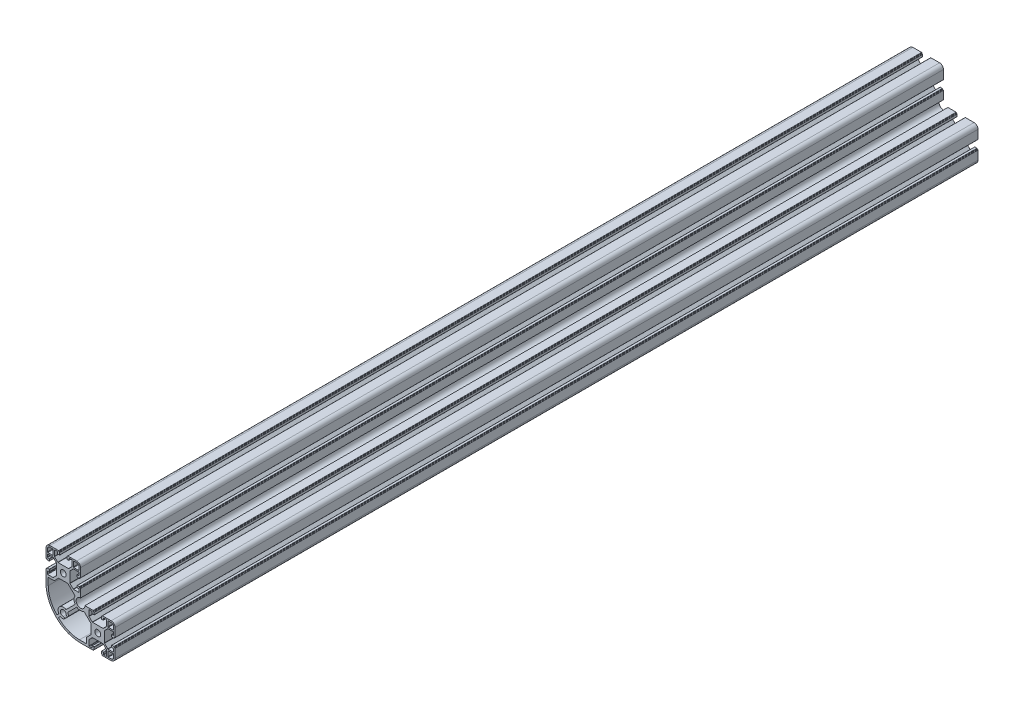
SolidWorks part; units mm, degrees
material "6063 T5"
ref_plane "Спереди" through (0, 0, 0) normal (0, 0, 1) x (1, 0, 0)
ref_plane "Сверху" through (0, 0, 0) normal (0, 1, 0) x (1, 0, 0)
ref_plane "Справа" through (0, 0, 0) normal (1, 0, 0) x (0, 0, -1)
sketch "Эскиз1" plane through (0, 0, 0) normal (0, 0, 1) x (1, 0, 0)
  line L0 (-19.98, 20.5457) -> (20.02, 20.5457) construction
  line L1 (-20, 10.25) -> (-20, 15.5)
  line L2 (-15.5, 20) -> (-10.25, 20)
  line L3 (10.25, 20) -> (15.5, 20)
  line L4 (-12.3, 11.8) -> (-17.8, 11.8)
  line L5 (-11.8, 12.3) -> (-11.8, 17.8)
  line L6 (-12.3, 18.3) -> (-15.5, 18.3)
  line L7 (-18.3, 12.3) -> (-18.3, 15.5)
  line L8 (20, 15.5) -> (20, 10.25)
  line L9 (11.8, 12.3) -> (11.8, 17.8)
  line L10 (12.3, 11.8) -> (17.8, 11.8)
  line L11 (18.3, 12.3) -> (18.3, 15.5)
  line L12 (12.3, 18.3) -> (15.5, 18.3)
  line L13 (0, 0) -> (0, -40) construction
  line L14 (0, -40) -> (40, -40) construction
  line L19 (0, -40) -> (40, 0) construction
  line L20 (0, 0) -> (-20, -10.25) construction
  line L25 (0, 0) -> (-11.8, 12.3) construction
  line L26 (0, 0) -> (12.3, 11.8) construction
  line L27 (60, -55.5) -> (60, -50.25)
  line L28 (50.25, -60) -> (55.5, -60)
  line L29 (58.3, -52.3) -> (58.3, -55.5)
  line L30 (52.3, -58.3) -> (55.5, -58.3)
  line L31 (51.8, -52.3) -> (51.8, -57.8)
  line L32 (52.3, -51.8) -> (57.8, -51.8)
  line L33 (51.8, -27.7) -> (51.8, -22.2)
  line L34 (52.3, -21.7) -> (55.5, -21.7)
  line L35 (58.3, -27.7) -> (58.3, -24.5)
  line L36 (52.3, -28.2) -> (57.8, -28.2)
  line L37 (55.5, -20) -> (50.25, -20)
  line L38 (0, 0) -> (-10.25, 20) construction
  line L39 (60, -29.75) -> (60, -24.5)
  line L40 (-19.9447, 33.6) -> (60.0553, 33.6) construction
  line L41 (-20, -10.25) -> (-20, -20)
  line L42 (20, -60) -> (29.75, -60)
  line L43 (-17.4, -12.85) -> (-17.4, -21.15)
  line L44 (-7.3211, -45.4826) -> (-5.0611, -43.2226)
  line L45 (-17.4, -12.85) -> (-10.623, -12.85)
  line L46 (-10.623, -12.85) -> (-5.373, -7.6)
  line L47 (-5.373, -7.6) -> (5.373, -7.6)
  line L48 (5.373, -7.6) -> (13.7014, -15.9284)
  line L49 (20, -10.25) -> (20, -14.9)
  line L50 (25.1, -20) -> (29.75, -20)
  line L51 (3.2226, -34.9389) -> (13.8577, -24.3038)
  line L52 (-5.4826, -47.3211) -> (-3.2226, -45.0611)
  line L53 (27.15, -57.4) -> (18.85, -57.4)
  line L54 (27.15, -57.4) -> (27.15, -50.623)
  line L55 (27.15, -50.623) -> (32.4, -45.373)
  line L56 (32.4, -45.373) -> (32.4, -34.627)
  line L57 (32.4, -34.627) -> (24.0716, -26.2986)
  line L58 (5.0611, -36.7774) -> (15.6962, -26.1423)
  arc A0 (-20, 15.5) -> (-15.5, 20) centre (-15.5, 15.5) cw
  arc A1 (-15.5, 18.3) -> (-18.3, 15.5) centre (-15.5, 15.5) ccw
  arc A2 (-17.8, 11.8) -> (-18.3, 12.3) centre (-17.8, 12.3) cw
  arc A3 (-12.3, 11.8) -> (-11.8, 12.3) centre (-12.3, 12.3) ccw
  arc A4 (-11.8, 17.8) -> (-12.3, 18.3) centre (-12.3, 17.8) ccw
  circle A5 centre (0, 0) radius 3.4
  arc A6 (15.5, 20) -> (20, 15.5) centre (15.5, 15.5) cw
  arc A7 (18.3, 15.5) -> (15.5, 18.3) centre (15.5, 15.5) ccw
  arc A8 (11.8, 17.8) -> (12.3, 18.3) centre (12.3, 17.8) cw
  arc A9 (11.8, 12.3) -> (12.3, 11.8) centre (12.3, 12.3) ccw
  arc A10 (17.8, 11.8) -> (18.3, 12.3) centre (17.8, 12.3) ccw
  circle A11 centre (40, -40) radius 3.4
  arc A16 (55.5, -60) -> (60, -55.5) centre (55.5, -55.5) ccw
  arc A21 (58.3, -55.5) -> (55.5, -58.3) centre (55.5, -55.5) cw
  arc A22 (51.8, -57.8) -> (52.3, -58.3) centre (52.3, -57.8) ccw
  arc A23 (51.8, -52.3) -> (52.3, -51.8) centre (52.3, -52.3) cw
  arc A24 (57.8, -51.8) -> (58.3, -52.3) centre (57.8, -52.3) cw
  arc A25 (52.3, -28.2) -> (51.8, -27.7) centre (52.3, -27.7) cw
  arc A26 (51.8, -22.2) -> (52.3, -21.7) centre (52.3, -22.2) cw
  arc A27 (55.5, -21.7) -> (58.3, -24.5) centre (55.5, -24.5) cw
  arc A28 (57.8, -28.2) -> (58.3, -27.7) centre (57.8, -27.7) ccw
  arc A29 (60, -24.5) -> (55.5, -20) centre (55.5, -24.5) ccw
  arc A30 (-20, -20) -> (20, -60) centre (20, -20) ccw
  arc A31 (-17.4, -21.15) -> (-7.3211, -45.4826) centre (17.0115, -21.15) ccw
  arc A32 (20, -14.9) -> (25.1, -20) centre (20, -20) ccw
  arc A33 (13.7014, -15.9284) -> (13.8577, -24.3038) centre (20, -20) ccw
  arc A34 (-5.0611, -43.2226) -> (3.2226, -34.9389) centre (0, -40) cw
  arc A36 (18.85, -57.4) -> (-5.4826, -47.3211) centre (18.85, -22.9885) cw
  arc A37 (24.0716, -26.2986) -> (15.6962, -26.1423) centre (20, -20) cw
  arc A38 (0, -43.4) -> (3.4, -40) centre (0, -40) cw
  arc A39 (3.4, -40) -> (6, -40) centre (4.7, -40) ccw
  arc A40 (5.0611, -36.7774) -> (6, -40) centre (0, -40) cw
  arc A41 (-3.2226, -45.0611) -> (0, -46) centre (0, -40) ccw
  arc A42 (0, -43.4) -> (0, -46) centre (0, -44.7) cw
  point P5 (0, 0)
  point P23 (0, 0)
  point P103 (0, -7.6)
  line B0 (-20, 10.25) -> (-20, 5.4)
  line B1 (-19.7, 5.1) -> (-19.3, 5.1)
  line B2 (-19, 4.8) -> (-19, 4.4)
  line B3 (-18.7, 4.1) -> (-16.3, 4.1)
  line B4 (-16, 4.4) -> (-16, 6.3)
  line B5 (-16.3, 6.6) -> (-18, 6.6)
  line B6 (-18.5, 7.1) -> (-18.5, 9.75)
  line B7 (-18, 10.25) -> (-11.9071, 10.25)
  line B8 (-11.5536, 10.1036) -> (-7.8464, 6.3964)
  line B9 (-7.7, 6.0429) -> (-7.7, -6.0429)
  line B10 (-7.7, 0) -> (-20, 0) construction
  line B11 (-11.5536, -10.1036) -> (-7.8464, -6.3964)
  line B12 (-18, -10.25) -> (-11.9071, -10.25)
  line B13 (-18.5, -7.1) -> (-18.5, -9.75)
  line B14 (-16.3, -6.6) -> (-18, -6.6)
  line B15 (-16, -4.4) -> (-16, -6.3)
  line B16 (-18.7, -4.1) -> (-16.3, -4.1)
  line B17 (-19, -4.8) -> (-19, -4.4)
  line B18 (-19.7, -5.1) -> (-19.3, -5.1)
  line B19 (-20, -10.25) -> (-20, -5.4)
  arc B20 (-16, 6.3) -> (-16.3, 6.6) centre (-16.3, 6.3) ccw
  arc B21 (-16.3, 4.1) -> (-16, 4.4) centre (-16.3, 4.4) ccw
  arc B22 (-19, 4.4) -> (-18.7, 4.1) centre (-18.7, 4.4) ccw
  arc B23 (-19.3, 5.1) -> (-19, 4.8) centre (-19.3, 4.8) cw
  arc B24 (-20, 5.4) -> (-19.7, 5.1) centre (-19.7, 5.4) ccw
  arc B25 (-7.8464, 6.3964) -> (-7.7, 6.0429) centre (-8.2, 6.0429) cw
  arc B26 (-11.9071, 10.25) -> (-11.5536, 10.1036) centre (-11.9071, 9.75) cw
  arc B27 (-18.5, 9.75) -> (-18, 10.25) centre (-18, 9.75) cw
  arc B28 (-18, 6.6) -> (-18.5, 7.1) centre (-18, 7.1) cw
  arc B29 (-18, -6.6) -> (-18.5, -7.1) centre (-18, -7.1) ccw
  arc B30 (-18.5, -9.75) -> (-18, -10.25) centre (-18, -9.75) ccw
  arc B31 (-11.9071, -10.25) -> (-11.5536, -10.1036) centre (-11.9071, -9.75) ccw
  arc B32 (-7.8464, -6.3964) -> (-7.7, -6.0429) centre (-8.2, -6.0429) ccw
  arc B33 (-20, -5.4) -> (-19.7, -5.1) centre (-19.7, -5.4) cw
  arc B34 (-19.3, -5.1) -> (-19, -4.8) centre (-19.3, -4.8) ccw
  arc B35 (-19, -4.4) -> (-18.7, -4.1) centre (-18.7, -4.4) cw
  arc B36 (-16.3, -4.1) -> (-16, -4.4) centre (-16.3, -4.4) cw
  arc B37 (-16, -6.3) -> (-16.3, -6.6) centre (-16.3, -6.3) cw
  line B38 (10.25, 20) -> (5.4, 20)
  line B39 (5.1, 19.7) -> (5.1, 19.3)
  line B40 (4.8, 19) -> (4.4, 19)
  line B41 (4.1, 18.7) -> (4.1, 16.3)
  line B42 (4.4, 16) -> (6.3, 16)
  line B43 (6.6, 16.3) -> (6.6, 18)
  line B44 (7.1, 18.5) -> (9.75, 18.5)
  line B45 (10.25, 18) -> (10.25, 11.9071)
  line B46 (10.1036, 11.5536) -> (6.3964, 7.8464)
  line B47 (6.0429, 7.7) -> (-6.0429, 7.7)
  line B48 (0, 7.7) -> (0, 20) construction
  line B49 (-10.1036, 11.5536) -> (-6.3964, 7.8464)
  line B50 (-10.25, 18) -> (-10.25, 11.9071)
  line B51 (-7.1, 18.5) -> (-9.75, 18.5)
  line B52 (-6.6, 16.3) -> (-6.6, 18)
  line B53 (-4.4, 16) -> (-6.3, 16)
  line B54 (-4.1, 18.7) -> (-4.1, 16.3)
  line B55 (-4.8, 19) -> (-4.4, 19)
  line B56 (-5.1, 19.7) -> (-5.1, 19.3)
  line B57 (-10.25, 20) -> (-5.4, 20)
  arc B58 (6.3, 16) -> (6.6, 16.3) centre (6.3, 16.3) ccw
  arc B59 (4.1, 16.3) -> (4.4, 16) centre (4.4, 16.3) ccw
  arc B60 (4.4, 19) -> (4.1, 18.7) centre (4.4, 18.7) ccw
  arc B61 (5.1, 19.3) -> (4.8, 19) centre (4.8, 19.3) cw
  arc B62 (5.4, 20) -> (5.1, 19.7) centre (5.4, 19.7) ccw
  arc B63 (6.3964, 7.8464) -> (6.0429, 7.7) centre (6.0429, 8.2) cw
  arc B64 (10.25, 11.9071) -> (10.1036, 11.5536) centre (9.75, 11.9071) cw
  arc B65 (9.75, 18.5) -> (10.25, 18) centre (9.75, 18) cw
  arc B66 (6.6, 18) -> (7.1, 18.5) centre (7.1, 18) cw
  arc B67 (-6.6, 18) -> (-7.1, 18.5) centre (-7.1, 18) ccw
  arc B68 (-9.75, 18.5) -> (-10.25, 18) centre (-9.75, 18) ccw
  arc B69 (-10.25, 11.9071) -> (-10.1036, 11.5536) centre (-9.75, 11.9071) ccw
  arc B70 (-6.3964, 7.8464) -> (-6.0429, 7.7) centre (-6.0429, 8.2) ccw
  arc B71 (-5.4, 20) -> (-5.1, 19.7) centre (-5.4, 19.7) cw
  arc B72 (-5.1, 19.3) -> (-4.8, 19) centre (-4.8, 19.3) ccw
  arc B73 (-4.4, 19) -> (-4.1, 18.7) centre (-4.4, 18.7) cw
  arc B74 (-4.1, 16.3) -> (-4.4, 16) centre (-4.4, 16.3) cw
  arc B75 (-6.3, 16) -> (-6.6, 16.3) centre (-6.3, 16.3) cw
  line B76 (20, -10.25) -> (20, -5.4)
  line B77 (19.7, -5.1) -> (19.3, -5.1)
  line B78 (19, -4.8) -> (19, -4.4)
  line B79 (18.7, -4.1) -> (16.3, -4.1)
  line B80 (16, -4.4) -> (16, -6.3)
  line B81 (16.3, -6.6) -> (18, -6.6)
  line B82 (18.5, -7.1) -> (18.5, -9.75)
  line B83 (18, -10.25) -> (11.9071, -10.25)
  line B84 (11.5536, -10.1036) -> (7.8464, -6.3964)
  line B85 (7.7, -6.0429) -> (7.7, 6.0429)
  line B86 (7.7, 0) -> (20, 0) construction
  line B87 (11.5536, 10.1036) -> (7.8464, 6.3964)
  line B88 (18, 10.25) -> (11.9071, 10.25)
  line B89 (18.5, 7.1) -> (18.5, 9.75)
  line B90 (16.3, 6.6) -> (18, 6.6)
  line B91 (16, 4.4) -> (16, 6.3)
  line B92 (18.7, 4.1) -> (16.3, 4.1)
  line B93 (19, 4.8) -> (19, 4.4)
  line B94 (19.7, 5.1) -> (19.3, 5.1)
  line B95 (20, 10.25) -> (20, 5.4)
  arc B96 (16, -6.3) -> (16.3, -6.6) centre (16.3, -6.3) ccw
  arc B97 (16.3, -4.1) -> (16, -4.4) centre (16.3, -4.4) ccw
  arc B98 (19, -4.4) -> (18.7, -4.1) centre (18.7, -4.4) ccw
  arc B99 (19.3, -5.1) -> (19, -4.8) centre (19.3, -4.8) cw
  arc B100 (20, -5.4) -> (19.7, -5.1) centre (19.7, -5.4) ccw
  arc B101 (7.8464, -6.3964) -> (7.7, -6.0429) centre (8.2, -6.0429) cw
  arc B102 (11.9071, -10.25) -> (11.5536, -10.1036) centre (11.9071, -9.75) cw
  arc B103 (18.5, -9.75) -> (18, -10.25) centre (18, -9.75) cw
  arc B104 (18, -6.6) -> (18.5, -7.1) centre (18, -7.1) cw
  arc B105 (18, 6.6) -> (18.5, 7.1) centre (18, 7.1) ccw
  arc B106 (18.5, 9.75) -> (18, 10.25) centre (18, 9.75) ccw
  arc B107 (11.9071, 10.25) -> (11.5536, 10.1036) centre (11.9071, 9.75) ccw
  arc B108 (7.8464, 6.3964) -> (7.7, 6.0429) centre (8.2, 6.0429) ccw
  arc B109 (20, 5.4) -> (19.7, 5.1) centre (19.7, 5.4) cw
  arc B110 (19.3, 5.1) -> (19, 4.8) centre (19.3, 4.8) ccw
  arc B111 (19, 4.4) -> (18.7, 4.1) centre (18.7, 4.4) cw
  arc B112 (16.3, 4.1) -> (16, 4.4) centre (16.3, 4.4) cw
  arc B113 (16, 6.3) -> (16.3, 6.6) centre (16.3, 6.3) cw
  line B114 (29.75, -20) -> (34.6, -20)
  line B115 (34.9, -20.3) -> (34.9, -20.7)
  line B116 (35.2, -21) -> (35.6, -21)
  line B117 (35.9, -21.3) -> (35.9, -23.7)
  line B118 (35.6, -24) -> (33.7, -24)
  line B119 (33.4, -23.7) -> (33.4, -22)
  line B120 (32.9, -21.5) -> (30.25, -21.5)
  line B121 (29.75, -22) -> (29.75, -28.0929)
  line B122 (29.8964, -28.4464) -> (33.6036, -32.1536)
  line B123 (33.9571, -32.3) -> (46.0429, -32.3)
  line B124 (40, -32.3) -> (40, -20) construction
  line B125 (50.1036, -28.4464) -> (46.3964, -32.1536)
  line B126 (50.25, -22) -> (50.25, -28.0929)
  line B127 (47.1, -21.5) -> (49.75, -21.5)
  line B128 (46.6, -23.7) -> (46.6, -22)
  line B129 (44.4, -24) -> (46.3, -24)
  line B130 (44.1, -21.3) -> (44.1, -23.7)
  line B131 (44.8, -21) -> (44.4, -21)
  line B132 (45.1, -20.3) -> (45.1, -20.7)
  line B133 (50.25, -20) -> (45.4, -20)
  arc B134 (33.7, -24) -> (33.4, -23.7) centre (33.7, -23.7) cw
  arc B135 (35.9, -23.7) -> (35.6, -24) centre (35.6, -23.7) cw
  arc B136 (35.6, -21) -> (35.9, -21.3) centre (35.6, -21.3) cw
  arc B137 (34.9, -20.7) -> (35.2, -21) centre (35.2, -20.7) ccw
  arc B138 (34.6, -20) -> (34.9, -20.3) centre (34.6, -20.3) cw
  arc B139 (33.6036, -32.1536) -> (33.9571, -32.3) centre (33.9571, -31.8) ccw
  arc B140 (29.75, -28.0929) -> (29.8964, -28.4464) centre (30.25, -28.0929) ccw
  arc B141 (30.25, -21.5) -> (29.75, -22) centre (30.25, -22) ccw
  arc B142 (33.4, -22) -> (32.9, -21.5) centre (32.9, -22) ccw
  arc B143 (46.6, -22) -> (47.1, -21.5) centre (47.1, -22) cw
  arc B144 (49.75, -21.5) -> (50.25, -22) centre (49.75, -22) cw
  arc B145 (50.25, -28.0929) -> (50.1036, -28.4464) centre (49.75, -28.0929) cw
  arc B146 (46.3964, -32.1536) -> (46.0429, -32.3) centre (46.0429, -31.8) cw
  arc B147 (45.4, -20) -> (45.1, -20.3) centre (45.4, -20.3) ccw
  arc B148 (45.1, -20.7) -> (44.8, -21) centre (44.8, -20.7) cw
  arc B149 (44.4, -21) -> (44.1, -21.3) centre (44.4, -21.3) ccw
  arc B150 (44.1, -23.7) -> (44.4, -24) centre (44.4, -23.7) ccw
  arc B151 (46.3, -24) -> (46.6, -23.7) centre (46.3, -23.7) ccw
  line B152 (50.25, -60) -> (45.4, -60)
  line B153 (45.1, -59.7) -> (45.1, -59.3)
  line B154 (44.8, -59) -> (44.4, -59)
  line B155 (44.1, -58.7) -> (44.1, -56.3)
  line B156 (44.4, -56) -> (46.3, -56)
  line B157 (46.6, -56.3) -> (46.6, -58)
  line B158 (47.1, -58.5) -> (49.75, -58.5)
  line B159 (50.25, -58) -> (50.25, -51.9071)
  line B160 (50.1036, -51.5536) -> (46.3964, -47.8464)
  line B161 (46.0429, -47.7) -> (33.9571, -47.7)
  line B162 (40, -47.7) -> (40, -60) construction
  line B163 (29.8964, -51.5536) -> (33.6036, -47.8464)
  line B164 (29.75, -58) -> (29.75, -51.9071)
  line B165 (32.9, -58.5) -> (30.25, -58.5)
  line B166 (33.4, -56.3) -> (33.4, -58)
  line B167 (35.6, -56) -> (33.7, -56)
  line B168 (35.9, -58.7) -> (35.9, -56.3)
  line B169 (35.2, -59) -> (35.6, -59)
  line B170 (34.9, -59.7) -> (34.9, -59.3)
  line B171 (29.75, -60) -> (34.6, -60)
  arc B172 (46.3, -56) -> (46.6, -56.3) centre (46.3, -56.3) cw
  arc B173 (44.1, -56.3) -> (44.4, -56) centre (44.4, -56.3) cw
  arc B174 (44.4, -59) -> (44.1, -58.7) centre (44.4, -58.7) cw
  arc B175 (45.1, -59.3) -> (44.8, -59) centre (44.8, -59.3) ccw
  arc B176 (45.4, -60) -> (45.1, -59.7) centre (45.4, -59.7) cw
  arc B177 (46.3964, -47.8464) -> (46.0429, -47.7) centre (46.0429, -48.2) ccw
  arc B178 (50.25, -51.9071) -> (50.1036, -51.5536) centre (49.75, -51.9071) ccw
  arc B179 (49.75, -58.5) -> (50.25, -58) centre (49.75, -58) ccw
  arc B180 (46.6, -58) -> (47.1, -58.5) centre (47.1, -58) ccw
  arc B181 (33.4, -58) -> (32.9, -58.5) centre (32.9, -58) cw
  arc B182 (30.25, -58.5) -> (29.75, -58) centre (30.25, -58) cw
  arc B183 (29.75, -51.9071) -> (29.8964, -51.5536) centre (30.25, -51.9071) cw
  arc B184 (33.6036, -47.8464) -> (33.9571, -47.7) centre (33.9571, -48.2) cw
  arc B185 (34.6, -60) -> (34.9, -59.7) centre (34.6, -59.7) ccw
  arc B186 (34.9, -59.3) -> (35.2, -59) centre (35.2, -59.3) cw
  arc B187 (35.6, -59) -> (35.9, -58.7) centre (35.6, -58.7) ccw
  arc B188 (35.9, -56.3) -> (35.6, -56) centre (35.6, -56.3) ccw
  arc B189 (33.7, -56) -> (33.4, -56.3) centre (33.7, -56.3) ccw
  line B190 (60, -29.75) -> (60, -34.6)
  line B191 (59.7, -34.9) -> (59.3, -34.9)
  line B192 (59, -35.2) -> (59, -35.6)
  line B193 (58.7, -35.9) -> (56.3, -35.9)
  line B194 (56, -35.6) -> (56, -33.7)
  line B195 (56.3, -33.4) -> (58, -33.4)
  line B196 (58.5, -32.9) -> (58.5, -30.25)
  line B197 (58, -29.75) -> (51.9071, -29.75)
  line B198 (51.5536, -29.8964) -> (47.8464, -33.6036)
  line B199 (47.7, -33.9571) -> (47.7, -46.0429)
  line B200 (47.7, -40) -> (60, -40) construction
  line B201 (51.5536, -50.1036) -> (47.8464, -46.3964)
  line B202 (58, -50.25) -> (51.9071, -50.25)
  line B203 (58.5, -47.1) -> (58.5, -49.75)
  line B204 (56.3, -46.6) -> (58, -46.6)
  line B205 (56, -44.4) -> (56, -46.3)
  line B206 (58.7, -44.1) -> (56.3, -44.1)
  line B207 (59, -44.8) -> (59, -44.4)
  line B208 (59.7, -45.1) -> (59.3, -45.1)
  line B209 (60, -50.25) -> (60, -45.4)
  arc B210 (56, -33.7) -> (56.3, -33.4) centre (56.3, -33.7) cw
  arc B211 (56.3, -35.9) -> (56, -35.6) centre (56.3, -35.6) cw
  arc B212 (59, -35.6) -> (58.7, -35.9) centre (58.7, -35.6) cw
  arc B213 (59.3, -34.9) -> (59, -35.2) centre (59.3, -35.2) ccw
  arc B214 (60, -34.6) -> (59.7, -34.9) centre (59.7, -34.6) cw
  arc B215 (47.8464, -33.6036) -> (47.7, -33.9571) centre (48.2, -33.9571) ccw
  arc B216 (51.9071, -29.75) -> (51.5536, -29.8964) centre (51.9071, -30.25) ccw
  arc B217 (58.5, -30.25) -> (58, -29.75) centre (58, -30.25) ccw
  arc B218 (58, -33.4) -> (58.5, -32.9) centre (58, -32.9) ccw
  arc B219 (58, -46.6) -> (58.5, -47.1) centre (58, -47.1) cw
  arc B220 (58.5, -49.75) -> (58, -50.25) centre (58, -49.75) cw
  arc B221 (51.9071, -50.25) -> (51.5536, -50.1036) centre (51.9071, -49.75) cw
  arc B222 (47.8464, -46.3964) -> (47.7, -46.0429) centre (48.2, -46.0429) cw
  arc B223 (60, -45.4) -> (59.7, -45.1) centre (59.7, -45.4) ccw
  arc B224 (59.3, -45.1) -> (59, -44.8) centre (59.3, -44.8) cw
  arc B225 (59, -44.4) -> (58.7, -44.1) centre (58.7, -44.4) ccw
  arc B226 (56.3, -44.1) -> (56, -44.4) centre (56.3, -44.4) ccw
  arc B227 (56, -46.3) -> (56.3, -46.6) centre (56.3, -46.3) ccw
  dimension "D12" = 40
  dimension "D13" = 10.2
  dimension "D2" = 4.5
  dimension "D3" = 2.8
  dimension "D5" = 0.5
  dimension "D6" = 6.8
  dimension "D14" = 7.5
  dimension "D19" = 6
  dimension "D22" = 6.8
  dimension "D1" = 2
  dimension "D4" = 6.5
  dimension "D7" = 20
  dimension "D8" = 40
  dimension "D9" = 80
  dimension "D10" = 90
  dimension "D11" = 90
  dimension "D15" = 2.6
  dimension "D16" = 2.6
  dimension "D17" = 2.6
  dimension "D18" = 7.6
  dimension "D20" = 1.3
  dimension "D21" = 8.3
sketch_block_instance "8B(20,5PL)-1"
sketch_block "8B(20,5PL)" parameters "D7"=0.3, "D8"=0.5, "D1"=12.3, "D2"=4, "D3"=8.2, "D4"=20.5, "D5"=10.2, "D6"=135, "D9"=4.85, "D10"=1.2, "D11"=2.15, "D12"=11.8
sketch_block_instance "8B(20,5PL)-3"
sketch_block_instance "8B(20,5PL)-4"
sketch_block_instance "8B(20,5PL)-13"
sketch_block_instance "8B(20,5PL)-14"
sketch_block_instance "8B(20,5PL)-15"
extrude "Бобышка-Вытянуть1" add sketch "Эскиз1" along normal blind 1000
